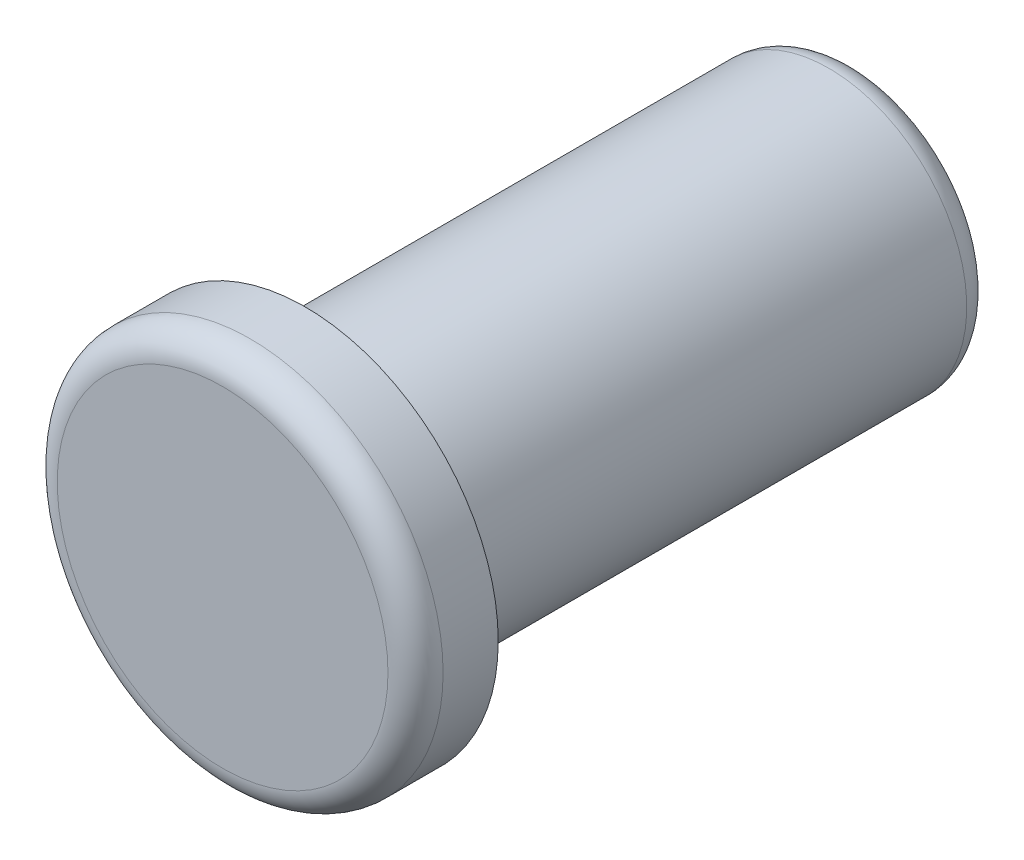
SolidWorks part; units mm, degrees
ref_plane "Přední rovina" through (0, 0, 0) normal (0, 0, 1) x (1, 0, 0)
ref_plane "Vrchní rovina" through (0, 0, 0) normal (0, 1, 0) x (1, 0, 0)
ref_plane "Pravá rovina" through (0, 0, 0) normal (1, 0, 0) x (0, 0, -1)
sketch "Skica1" plane through (0, 0, 0) normal (0, 0, 1) x (1, 0, 0)
  circle A0 centre (0, 0) radius 7
  dimension "D1" = 14
extrude "Přidat vysunutím1" add sketch "Skica1" along normal blind 3
sketch "Skica2" plane through (0, 0, 0) normal (0, 0, -1) x (-1, 0, 0)
  circle A0 centre (0, 0) radius 5
  dimension "D1" = 10
extrude "Přidat vysunutím2" add sketch "Skica2" along normal blind 20
fillet "Zaoblit1" radius 1 2 edges at (7, 0, 3) (-5, 0, -20)
